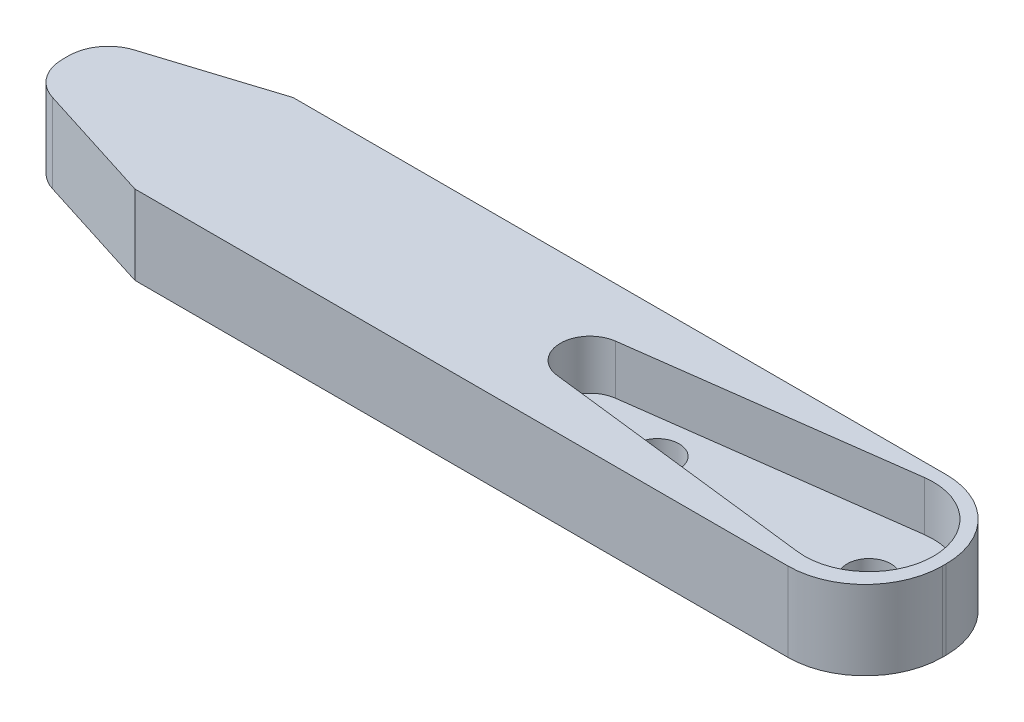
SolidWorks part; units mm, degrees
ref_plane "Front" through (0, 0, 0) normal (0, 0, 1) x (1, 0, 0)
ref_plane "Top" through (0, 0, 0) normal (0, 1, 0) x (1, 0, 0)
ref_plane "Right" through (0, 0, 0) normal (1, 0, 0) x (0, 0, -1)
sketch "草图1" plane through (0, 0, 0) normal (0, 1, 0) x (1, 0, 0)
  line L32 (-22.0065, 2.0684) -> (-15.9, 4)
  line L35 (-15.9, 4) -> (17.1, 4)
  line L36 (-23.4033, 0.1615) -> (-23.4033, -0.1615)
  line L39 (-15.9, -4) -> (17.1, -4)
  line L40 (21, 0.1) -> (21, -0.1)
  line L41 (18.8425, -3.5891) -> (21, -4) construction
  line L42 (18.8425, 3.5891) -> (21, 4) construction
  line L43 (-8.0732, 0) -> (6.8689, 0) construction
  line L44 (-22.0065, -2.0684) -> (-15.9, -4)
  arc A4 (17.1, 4) -> (21, 0.1) centre (17.1, 0.1) cw
  arc A5 (17.1, -4) -> (21, -0.1) centre (17.1, -0.1) ccw
  arc A6 (-22.0065, -2.0684) -> (-23.4033, -0.1615) centre (-21.4033, -0.1615) cw
  arc A7 (-22.0065, 2.0684) -> (-23.4033, 0.1615) centre (-21.4033, 0.1615) ccw
  point P0 (0, 0)
  point P1 (0, 0)
  point P3 (0, 0)
  point P22 (-23.4033, -1.6266)
  point P25 (-23.4033, 1.6266)
  dimension "D1" = 8
  dimension "D2" = 33
  dimension "D3" = 3.9
  dimension "D4" = 162.447
  dimension "D5" = 2
  dimension "D6" = 6.1065
extrude "凸台-拉伸1" add sketch "草图1" along normal blind 4
sketch "草图2" plane through (0, 4, 0) normal (0, 1, 0) x (1, 0, 0)
  line L0 (2.9019, 1.4869) -> (16.6707, 3.3215)
  line L1 (1.6475, -0.0104) -> (14.8621, 0.084) construction
  line L2 (2.9231, -1.4895) -> (16.7168, -3.1273)
  arc A0 (16.7168, -3.1273) -> (16.6707, 3.3215) centre (17.1, 0.1) ccw
  arc A1 (2.9019, 1.4869) -> (2.9231, -1.4895) centre (3.1, 0) ccw
  dimension "D1" = 6.5
  dimension "D2" = 3
  dimension "D3" = 14
extrude "切除-拉伸1" cut sketch "草图2" against normal blind 2.5
sketch "草图4" plane through (0, 1.5, 0) normal (0, 1, 0) x (1, 0, 0)
  circle A0 centre (17.1, 0.1) radius 1.1
  circle A1 centre (6.5, 0) radius 1.1
  dimension "D1" = 10.6
extrude "切除-拉伸2" cut sketch "草图4" against normal blind 1
